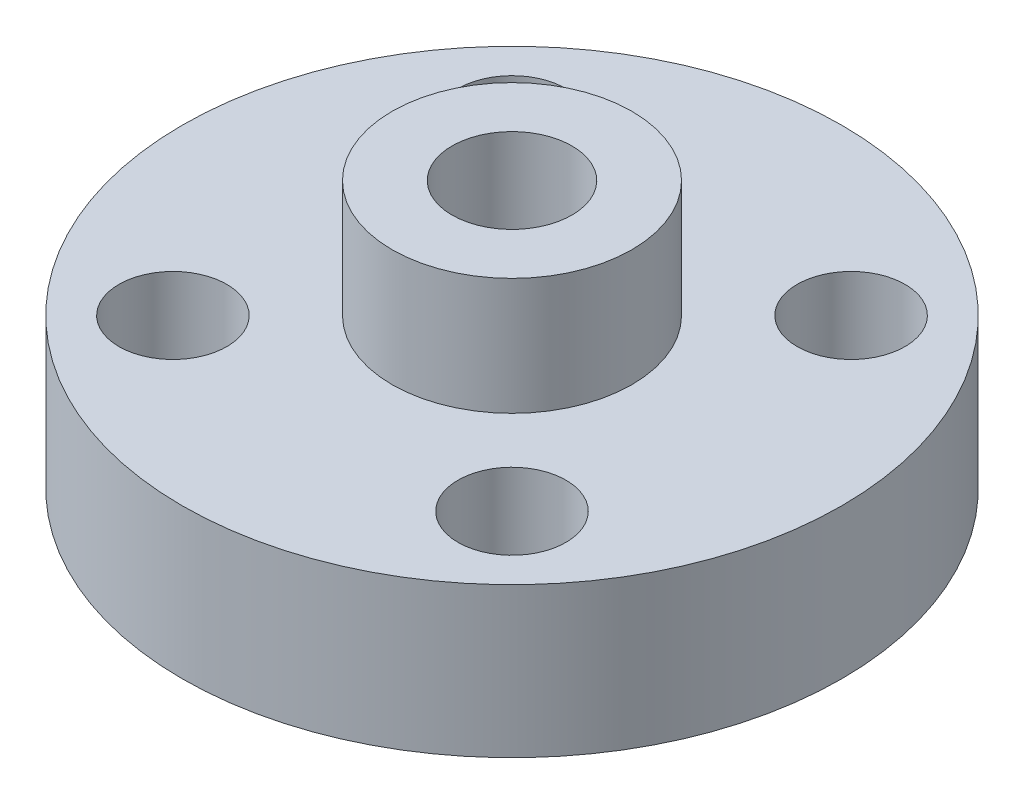
SolidWorks part; units mm, degrees
ref_plane "Front Plane" through (0, 0, 0) normal (0, 0, 1) x (1, 0, 0)
ref_plane "Top Plane" through (0, 0, 0) normal (0, 1, 0) x (1, 0, 0)
ref_plane "Right Plane" through (0, 0, 0) normal (1, 0, 0) x (0, 0, -1)
sketch "스케치1" plane through (0, 0, 0) normal (0, 1, 0) x (1, 0, 0)
  circle A0 centre (0, 0) radius 11
extrude "보스-돌출1" add sketch "스케치1" along normal blind 5
sketch "스케치2" plane through (0, 5, 0) normal (0, 1, 0) x (1, 0, 0)
  circle A0 centre (0, 0) radius 4
extrude "보스-돌출2" add sketch "스케치2" along normal blind 3.9
sketch "스케치3" plane through (0, 5, 0) normal (0, 1, 0) x (1, 0, 0)
  line L0 (0, 0) -> (-50000, 0) construction
  line L1 (0, 0) -> (35355.3391, 35355.3391) construction
  line L2 (0, 0) -> (35355.3391, -35355.3391) construction
  circle A0 centre (0, 0) radius 8 construction
  circle A1 centre (5.6569, 5.6569) radius 1.8
  circle A2 centre (-5.6569, -5.6569) radius 1.8
  circle A3 centre (-5.6569, 5.6569) radius 1.8
  circle A4 centre (5.6569, -5.6569) radius 1.8
extrude "컷-돌출1" cut sketch "스케치3" against normal through all
sketch "스케치4" plane through (0, 8.9, 0) normal (0, 1, 0) x (1, 0, 0)
  circle A0 centre (0, 0) radius 2
extrude "컷-돌출2" cut sketch "스케치4" against normal through all
sketch "스케치6" plane through (0, 0, 0) normal (0, 0, 1) x (1, 0, 0)
  line L0 (-11, 0) -> (11, 0) construction
  circle A0 centre (0, 2.5) radius 1.25
  dimension "D2" = 2.5
  dimension "D1" = 2.5
extrude "컷-돌출3" cut sketch "스케치6" against normal blind 13
